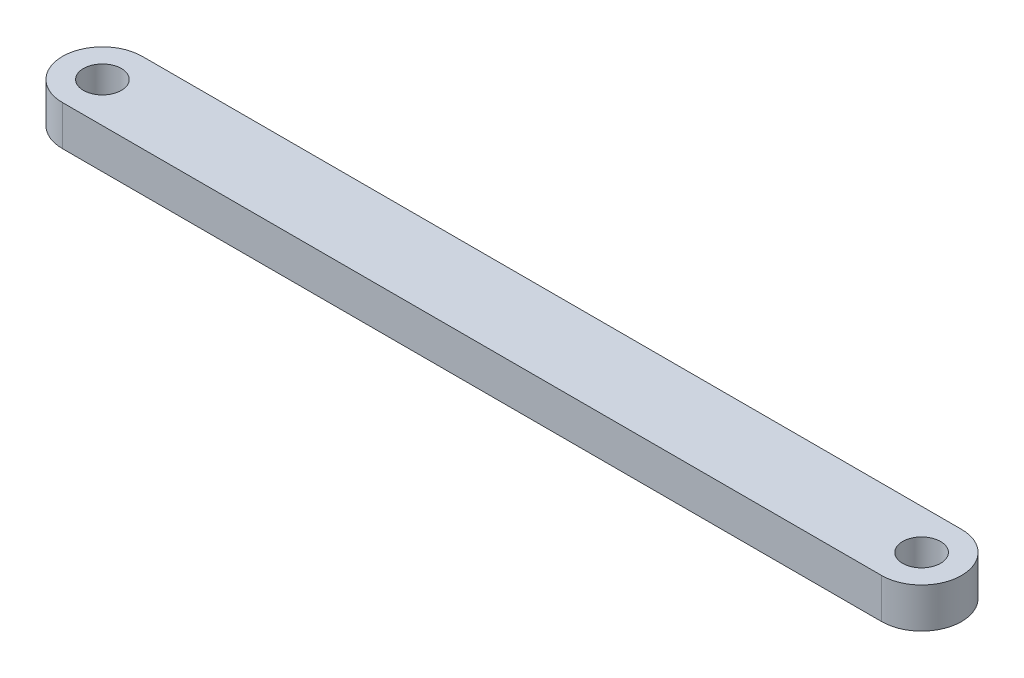
SolidWorks part; units mm, degrees
ref_plane "Front Plane" through (0, 0, 0) normal (0, 0, 1) x (1, 0, 0)
ref_plane "Top Plane" through (0, 0, 0) normal (0, 1, 0) x (1, 0, 0)
ref_plane "Right Plane" through (0, 0, 0) normal (1, 0, 0) x (0, 0, -1)
sketch "Sketch1" plane through (0, 0, 0) normal (0, 1, 0) x (1, 0, 0)
  line L0 (102.5, 0) -> (-102.5, 0) construction
  line L1 (102.5, -10) -> (-102.5, -10)
  line L2 (102.5, 10) -> (-102.5, 10)
  arc A0 (102.5, -10) -> (102.5, 10) centre (102.5, 0) ccw
  arc A1 (-102.5, 10) -> (-102.5, -10) centre (-102.5, 0) ccw
  circle A2 centre (-102.5, 0) radius 4.75
  circle A3 centre (102.5, 0) radius 4.75
  point P2 (0, 0)
  dimension "D2" = 10
  dimension "D3" = 9.5
  dimension "D4" = 9.5
  dimension "D1" = 205
extrude "Boss-Extrude1" add sketch "Sketch1" along normal blind 10
